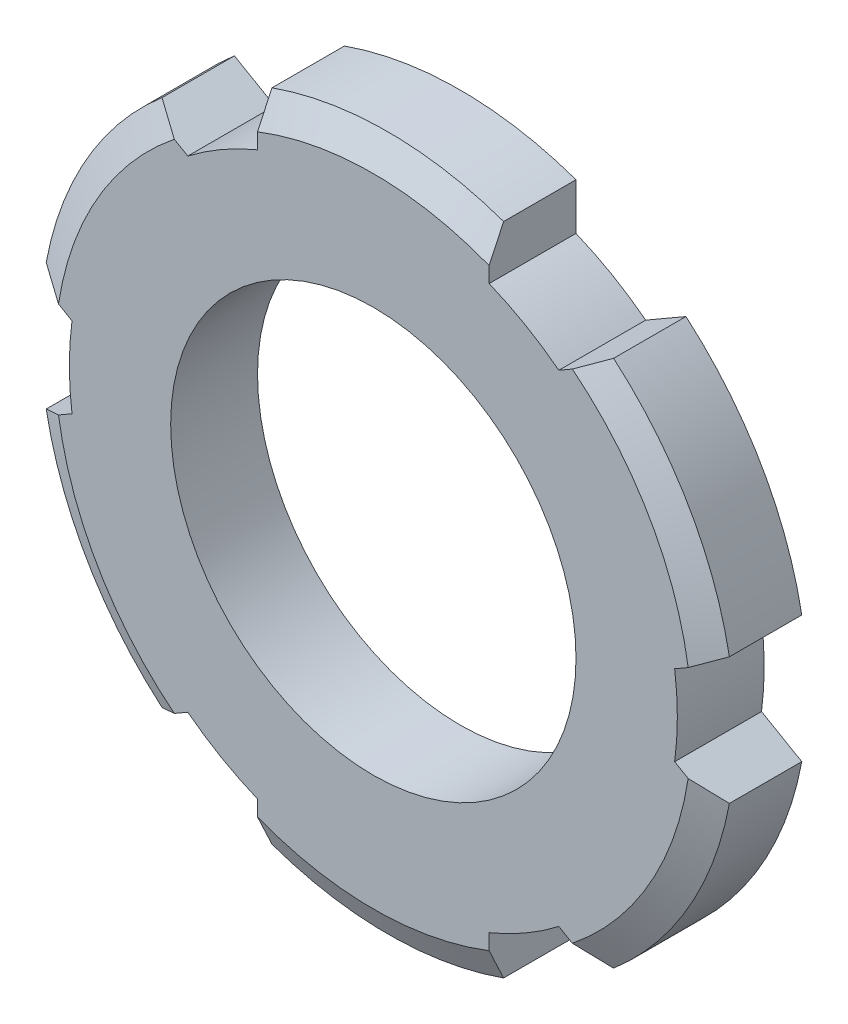
SolidWorks part; units mm, degrees
material "Alliage 7079"
ref_plane "Face" through (0, 0, 0) normal (0, 0, 1) x (1, 0, 0)
ref_plane "Dessus" through (0, 0, 0) normal (0, 1, 0) x (1, 0, 0)
ref_plane "Droite" through (0, 0, 0) normal (1, 0, 0) x (0, 0, -1)
sketch "Esquisse1" plane through (0, 0, 0) normal (0, 0, 1) x (1, 0, 0)
  line L0 (0, 0) -> (0, 16.7067) construction
  line L1 (7.798, 9.121) -> (6.4076, 8.3182)
  line L2 (4, 11.3137) -> (4, 9.7082)
  line L3 (-4, 11.3137) -> (-4, 9.7082)
  line L4 (11.798, 2.1928) -> (10.4076, 1.39)
  line L5 (11.798, -2.1928) -> (10.4076, -1.39)
  line L6 (7.798, -9.121) -> (6.4076, -8.3182)
  line L7 (4, -11.3137) -> (4, -9.7082)
  line L8 (-4, -11.3137) -> (-4, -9.7082)
  line L9 (-7.798, -9.121) -> (-6.4076, -8.3182)
  line L10 (-11.798, -2.1928) -> (-10.4076, -1.39)
  line L11 (-11.798, 2.1928) -> (-10.4076, 1.39)
  line L12 (-7.798, 9.121) -> (-6.4076, 8.3182)
  arc A0 (6.4076, 8.3182) -> (4, 9.7082) centre (0, 0) ccw
  arc A1 (4, 11.3137) -> (-4, 11.3137) centre (0, 0) ccw
  arc A2 (11.798, 2.1928) -> (7.798, 9.121) centre (0, 0) ccw
  arc A3 (7.798, -9.121) -> (11.798, -2.1928) centre (0, 0) ccw
  arc A4 (-4, -11.3137) -> (4, -11.3137) centre (0, 0) ccw
  arc A5 (-11.798, -2.1928) -> (-7.798, -9.121) centre (0, 0) ccw
  arc A6 (-7.798, 9.121) -> (-11.798, 2.1928) centre (0, 0) ccw
  arc A7 (-4, 9.7082) -> (-6.4076, 8.3182) centre (0, 0) ccw
  arc A8 (-10.4076, 1.39) -> (-10.4076, -1.39) centre (0, 0) ccw
  arc A9 (-6.4076, -8.3182) -> (-4, -9.7082) centre (0, 0) ccw
  arc A10 (4, -9.7082) -> (6.4076, -8.3182) centre (0, 0) ccw
  arc A11 (10.4076, -1.39) -> (10.4076, 1.39) centre (0, 0) ccw
  dimension "D1" = 21
  dimension "D2" = 24
  dimension "D3" = 8
extrude "Extrusion1" add sketch "Esquisse1" along normal blind 3
hole_wizard "Trou taraudé M161" positions "Esquisse3" profile "Esquisse2" tap size "M16" standard "ISO" end condition through all
sketch "Esquisse3" plane through (0, 0, 3) normal (0, 0, 1) x (1, 0, 0)
  point P0 (0, 0)
sketch "Esquisse2" plane through (0, 0, 3) normal (1, 0, 0) x (0, -1, 0)
  line L0 (0, 0) -> (0, 3)
  line L1 (0, 3) -> (7, 3)
  line L2 (7, 3) -> (7, 0)
  line L5 (7, 0) -> (0, 0)
  line L11 (0, -6.35) -> (0, 107.95) construction
  dimension "Diamètre du trou pour taraudage jusqu'au prochain" = 14
  dimension "Profondeur du trou pour taraudage jusqu'au prochain" = 3
cosmetic thread "Filetage de perçage1" parameters "D2"=16
chamfer "Chanfrein2" distance 0.5 distance2 1 6 edges at (10.3923, 6, 3) (0, -12, 3) (10.3923, -6, 3) (-10.3923, -6, 3) (-10.3923, 6, 3) (0, 12, 3)
